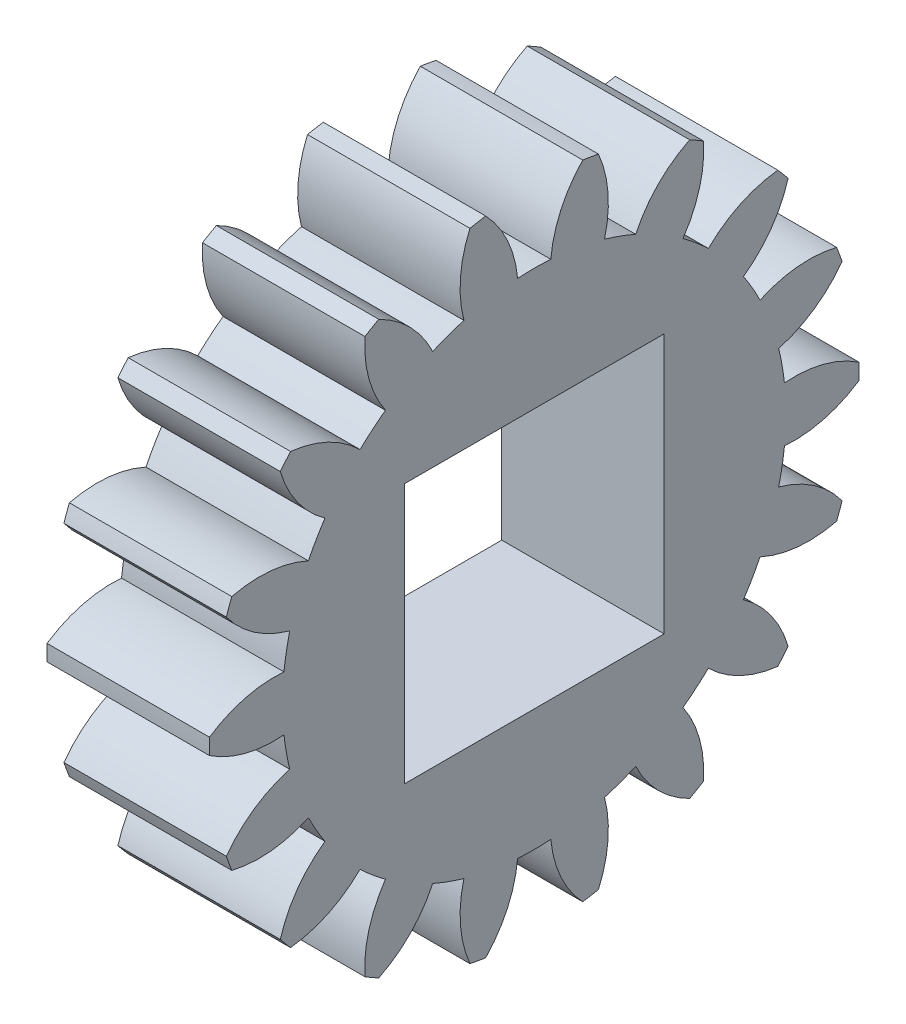
SolidWorks part; units mm, degrees
material "Plain Carbon Steel"
ref_plane "Plane1" through (0, 0, 0) normal (0, 0, 1) x (1, 0, 0)
ref_plane "Plane2" through (0, 0, 0) normal (0, 1, 0) x (1, 0, 0)
ref_plane "Plane3" through (0, 0, 0) normal (1, 0, 0) x (0, 0, -1)
sketch "HoldingSke" plane through (0, 0, 0) normal (0, 1, 0) x (1, 0, 0)
  line L0 (0, 0) -> (0.9511, -0.309)
  line L1 (-15, 0) -> (100, 0) construction
  line L2 (0, 0) -> (-2.1039, 2.3779)
  line L3 (0, 0) -> (-11.863, 4.5341)
  line L4 (0, 0) -> (8.2133, 2.6687)
  line L5 (0, 0) -> (-46.8476, -17.4728)
  line L6 (0, 0) -> (-4.1448, -2.7965)
  line L7 (-2.1039, 2.3779) -> (8.6586, 51.2059)
  line L8 (-76.2, 54.61) -> (-75.3, 54.61)
  line L9 (-71.009, 38.7566) -> (-53.1078, 45.2721)
  line L10 (-76.2, 71.12) -> (104.1128, 71.12)
  line L11 (0, 0) -> (-5, 0)
  line L12 (-76.2, 101.6) -> (-76.162, 101.6)
  line L13 (24.9733, 27.94) -> (52.9518, 28.4284)
  line L14 (24.9733, 27.94) -> (24.9743, 27.94)
  line L15 (24.9733, 27.94) -> (100.4006, 29.5858)
  line L16 (-63.627, -1) -> (-12.827, -1)
  circle A0 centre (0, 0) radius 2.5
  circle A1 centre (0, 0) radius 7.749
  circle A2 centre (0, 0) radius 37.5
  circle A3 centre (0, 0) radius 2.5
  dimension "MHD" = 15.498
  dimension "Hub_dia" = 75
  dimension "Bore" = 5
  dimension "MBD" = 5
  dimension "Num_teeth" = 18
  dimension "Pitch" = 1
  dimension "Overall_len" = 50
  dimension "Show_teeth" = 18
  dimension "Thickness" = 5
  dimension "OAL" = 50.0001
  dimension "T_dim" = 0.9
  dimension "Ap" = 20
  dimension "H" = 19.05
  dimension "Pitch_radius" = 180.3128
  dimension "Width" = 5
  dimension "Backlash" = 0.038
  dimension "Addendum_fac" = 1
  dimension "Dedendum_fac" = 1.25
  dimension "Clearance_fac" = 0.25
  dimension "Dedendum_add" = 0.001
  dimension "Module" = 1
sketch "BasProSke" plane through (0, 0, 0) normal (0, 1, 0) x (1, 0, 0)
  line L0 (-10, 0) -> (60, 0) construction
  line L1 (0, 0) -> (0, 10)
  line L2 (0, 0) -> (5, 0)
  line L3 (5, 0) -> (5, 10)
  line L4 (5, 10) -> (0, 10)
  dimension "Thickness" = 5
  dimension "Diameter" = 20
revolve "Base-Revolve" add sketch "BasProSke" angle 360 about L0
sketch "TooCutSke" plane through (0, 0, 0) normal (1, 0, 0) x (0, 0, -1)
  line L1 (0, 0) -> (0, 107) construction
  line L2 (0, 0) -> (-0.8509, 8.9597) construction
  line L3 (0, 0) -> (-3.1157, 17.6701) construction
  line L4 (-0.8509, 8.9597) -> (-1.5579, 8.835) construction
  arc A0 (0.5106, 7.7322) -> (-0.5106, 7.7322) centre (0, 0) ccw
  arc A1 (1.5152, 9.9102) -> (-1.5152, 9.9102) centre (0, 0) ccw
  circle A2 centre (0, 0) radius 9 construction
  circle A3 centre (0, 0) radius 8.4572 construction
  arc A4 (-0.5106, 7.7322) -> (-1.5152, 9.9102) centre (-4.0952, 7.3996) ccw
  arc A5 (1.5152, 9.9102) -> (0.5106, 7.7322) centre (4.0952, 7.3996) ccw
  dimension "Root_dia" = 15.498
  dimension "Overcut_dia" = 20.0508
  dimension "Pitch_dia" = 18
  dimension "Base_dia" = 16.9145
  dimension "Flank_rad" = 3.6
  dimension "Half_ang" = 10
  dimension "Half_CT" = 0.7179
extrude "ToothCut" cut sketch "TooCutSke" along normal through all
fillet "Breaks" [suppressed] radius 0.02
fillet "RootFillets" [suppressed] radius 0.251
pattern_circular "TeethCuts" count 18 every 20 about axis through (-10, 0, 0) along (1, 0, 0) of "ToothCut", "RootFillets", "Breaks"
sketch "HubNeaOneSke" plane through (0, 0, 0) normal (-1, 0, 0) x (0, 0, 1)
  circle A0 centre (0, 0) radius 7.749
  dimension "Diameter" = 15.498
extrude "HubNearOne" [suppressed] add sketch "HubNeaOneSke" along normal blind 45.0001
sketch "HubNeaBotSke" plane through (0, 0, 0) normal (-1, 0, 0) x (0, 0, 1)
  circle A0 centre (0, 0) radius 7.749
  dimension "Diameter" = 15.498
extrude "HubNearBoth" [suppressed] add sketch "HubNeaBotSke" along normal blind 22.5
ref_plane "FarPln" through (5, 0, 0) normal (1, 0, 0) x (0, 0, -1)
sketch "HubFarSke" plane through (5, 0, 0) normal (1, 0, 0) x (0, 0, -1)
  circle A0 centre (0, 0) radius 7.749
  dimension "Diameter" = 15.498
extrude "HubFar" [suppressed] add sketch "HubFarSke" along normal blind 22.5
sketch "BorSke" plane through (0, 0, 0) normal (1, 0, 0) x (0, 0, -1)
  circle A0 centre (0, 0) radius 2.5
  dimension "Diameter" = 5
extrude "Bore" cut sketch "BorSke" along normal mid plane 100.0001
sketch "KeySke" plane through (0, 0, 0) normal (1, 0, 0) x (0, 0, -1)
  line L0 (-1, 0) -> (-1, 3.4)
  line L1 (-1, 3.4) -> (1, 3.4)
  line L2 (1, 3.4) -> (1, 0)
  line L3 (0, 0) -> (0, 34) construction
  line L4 (-1, 0) -> (1, 0)
  dimension "Offset" = 3.4
  dimension "Width" = 2
extrude "Keyway" [suppressed] cut sketch "KeySke" along normal mid plane 100.0001
pattern_circular "Keyway2" [suppressed] count 2 every 90 about axis through (-10, 0, 0) along (1, 0, 0)
sketch "Sketch1" plane through (5, 0, 0) normal (1, 0, 0) x (0, 0, -1)
  line L1 (4, -4) -> (-4, -4)
  line L2 (4, -4) -> (4, 4)
  line L3 (4, 4) -> (-4, 4)
  line L4 (-4, -4) -> (-4, 4)
  line L5 (4, -4) -> (-4, 4) construction
  line L6 (4, 4) -> (-4, -4) construction
  point P0 (0, 0)
  dimension "D1" = 8
extrude "Cut-Extrude1" cut sketch "Sketch1" against normal through all
equation "' \"Module@HoldingSke\" = 6.35"
equation "' \"Num_teeth@HoldingSke\" = 12"
equation "' \"Ap@HoldingSke\" =  20"
equation "' \"Ap@HoldingSke\" = 20"
equation "' \"Width@HoldingSke\" = 0.5 * 25.4"
equation "' \"Hub_dia@HoldingSke\"= 1 * 25.4"
equation "' \"Hub_dia@HoldingSke\" = 1 * 25.4"
equation "' \"Overall_len@HoldingSke\" = 1.0 * 25.4"
equation "' \"Bore@HoldingSke\" = 0.75 * 25.4"
equation "' \"T_dim@HoldingSke\" = 0.1 * 25.4"
equation "' \"Width@KeySke\" = 0.25 * 25.4"
equation "' \"Show_teeth@HoldingSke\" = 13"
equation "' \"Backlash@HoldingSke\" = 0.009 * 25.4"
equation "' \"Addendum_fac@HoldingSke\" = 1.0"
equation "' \"Dedendum_fac@HoldingSke\" = 1.25"
equation "' \"Dedendum_add@HoldingSke\" = 0.00005 * 25.4"
equation "' \"Clearance_fac@HoldingSke\" = 0.25"
equation "\"Pitch@HoldingSke\" = 1 / \"Module@HoldingSke\""
equation "\"Overcut_dia@TooCutSke\" = (\"Num_teeth@HoldingSke\" + 2 * \"Addendum_fac@HoldingSke\") / \"Pitch@HoldingSke\" + 0.002 * 25.4"
equation "\"Pitch_dia@TooCutSke\" = \"Num_teeth@HoldingSke\" / \"Pitch@HoldingSke\""
equation "\"Base_dia@TooCutSke\" = \"Num_teeth@HoldingSke\" / \"Pitch@HoldingSke\" * cos((\"Ap@HoldingSke\"  * 3.14159265 / 180))"
equation "\"Root_dia@TooCutSke\" = (\"Num_teeth@HoldingSke\" + 2) / \"Pitch@HoldingSke\" - 2 * (\"Addendum_fac@HoldingSke\" + \"Dedendum_fac@HoldingSke\") / \"Pitch@HoldingSke\" - \"Dedendum_add@HoldingSke\" * 2"
equation "\"Half_ang@TooCutSke\" = 180 / \"Num_teeth@HoldingSke\""
equation "\"Half_CT@TooCutSke\" = \"Num_teeth@HoldingSke\" / \"Pitch@HoldingSke\" * sin((3.14159265 / 2 / \"Num_teeth@HoldingSke\")) / 2 - 7 * \"Backlash@HoldingSke\" / 4"
equation "\"Flank_rad@TooCutSke\" = \"Num_teeth@HoldingSke\" / \"Pitch@HoldingSke\" / 5"
equation "\"Radius@RootFillets\" = \"Clearance_fac@HoldingSke\" / \"Pitch@HoldingSke\" + \"Dedendum_add@HoldingSke\""
equation "\"Break_rad@Breaks\" = 0.02 / \"Pitch@HoldingSke\""
equation "\"Thickness@HoldingSke\" = \"Width@HoldingSke\""
equation "\"OAL@HoldingSke\" = \"Thickness@HoldingSke\""
equation "\"MHD@HoldingSke\" = (\"Num_teeth@HoldingSke\" + 2) / \"Pitch@HoldingSke\" - 2 * (\"Addendum_fac@HoldingSke\" + \"Dedendum_fac@HoldingSke\")  / \"Pitch@HoldingSke\" - \"Dedendum_add@HoldingSke\" * 2"
equation "\"MBD@HoldingSke\" = (\"Num_teeth@HoldingSke\" + 2) / \"Pitch@HoldingSke\" - 2 * (\"Addendum_fac@HoldingSke\" + \"Dedendum_fac@HoldingSke\")  / \"Pitch@HoldingSke\" - \"Dedendum_add@HoldingSke\" * 2 - 0.002 * 25.4"
equation "\"MHD@HoldingSke\" = ((sgn( \"MHD@HoldingSke\" - \"Hub_dia@HoldingSke\" )-1)*( \"MHD@HoldingSke\" - \"Hub_dia@HoldingSke\" ))/-2+ \"Hub_dia@HoldingSke\""
equation "\"MBD@HoldingSke\" = ((sgn( \"MBD@HoldingSke\" - \"Bore@HoldingSke\" )-1)*( \"MBD@HoldingSke\" - \"Bore@HoldingSke\" ))/-2+ \"Bore@HoldingSke\""
equation "\"OAL@HoldingSke\" = ((sgn( \"OAL@HoldingSke\" - \"Overall_len@HoldingSke\" )+1)*( \"OAL@HoldingSke\" - \"Overall_len@HoldingSke\" ))/2 + \"Overall_len@HoldingSke\" + 0.000002 * 25.4"
equation "\"Num_teeth@TeethCuts\" = int( \"Show_teeth@HoldingSke\" ) + 1"
equation "\"Num_teeth@TeethCuts\" = ((sgn( \"Num_teeth@TeethCuts\" - \"Num_teeth@HoldingSke\" )-1)*( \"Num_teeth@TeethCuts\" - \"Num_teeth@HoldingSke\" ))/-2+ \"Num_teeth@HoldingSke\""
equation "\"Num_teeth@TeethCuts\" = ((sgn( \"Num_teeth@TeethCuts\" - 2.0)+1)*( \"Num_teeth@TeethCuts\" - 2.0))/2 +2.0"
equation "\"Angle@TeethCuts\" = 360.0 / \"Num_teeth@HoldingSke\""
equation "\"Diameter@BasProSke\" = (\"Num_teeth@HoldingSke\" + 2 * \"Addendum_fac@HoldingSke\") / \"Pitch@HoldingSke\""
equation "\"Thickness@BasProSke\"  = \"Thickness@HoldingSke\""
equation "' \"Fillet_rad@BasProSke\" =  \"Thickness@HoldingSke\" * 0.05"
equation "' \"Fillet_rad@BasProSke\" = \"Thickness@HoldingSke\" * 0.05"
equation "\"MHD@HoldingSke\" = ((sgn( \"MHD@HoldingSke\" - \"Root_dia@TooCutSke\" )-1)*( \"MHD@HoldingSke\" - \"Root_dia@TooCutSke\" ))/-2+ \"Root_dia@TooCutSke\""
equation "\"Diameter@HubNeaOneSke\" = \"MHD@HoldingSke\""
equation "\"Length@HubNearOne\" = \"OAL@HoldingSke\" - \"Thickness@BasProSke\""
equation "\"Diameter@HubNeaBotSke\" = \"MHD@HoldingSke\""
equation "\"Length@HubNearBoth\" = ( \"OAL@HoldingSke\" - \"Thickness@BasProSke\" ) / 2.0"
equation "\"Thickness@FarPln\" = \"Thickness@BasProSke\""
equation "\"Diameter@HubFarSke\" = \"MHD@HoldingSke\""
equation "\"Length@HubFar\" = ( \"OAL@HoldingSke\" - \"Thickness@BasProSke\" ) / 2.0"
equation "\"Diameter@BorSke\" = \"MBD@HoldingSke\""
equation "\"D1@Bore\" = \"OAL@HoldingSke\" * 2.0"
equation "\"D1@Keyway\" = \"OAL@HoldingSke\" * 2.0"
equation "\"Offset@KeySke\" = \"T_dim@HoldingSke\" + \"MBD@HoldingSke\" / 2.0"
